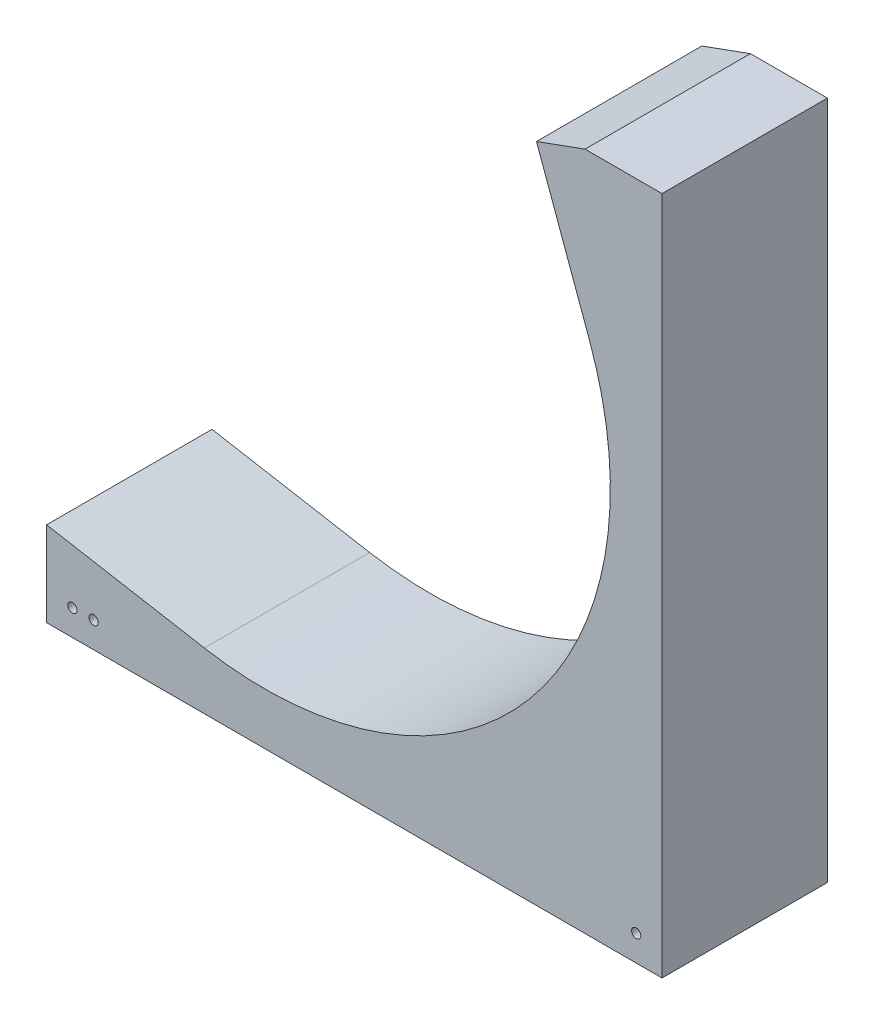
SolidWorks part; units mm, degrees
ref_plane "Front Plane" through (0, 0, 0) normal (0, 0, 1) x (1, 0, 0)
ref_plane "Top Plane" through (0, 0, 0) normal (0, 1, 0) x (1, 0, 0)
ref_plane "Right Plane" through (0, 0, 0) normal (1, 0, 0) x (0, 0, -1)
sketch "Sketch2" plane through (0, 0, 0) normal (0, 0, 1) x (1, 0, 0)
  line L0 (0, 0) -> (69.3863, 0)
  line L1 (69.3863, 0) -> (61.2697, 22.3003)
  line L2 (0, -65.2018) -> (-81.9123, -65.2018) construction
  line L3 (-11.3222, -64.2112) -> (-111.3786, -46.5686)
  line L4 (61.2697, 22.3003) -> (48.2387, 58.1026)
  arc A0 (61.2697, 22.3003) -> (-11.3222, -64.2112) centre (0, 0) cw
  circle A1 centre (0, 0) radius 45.212 construction
  point P11 (-11.3222, -64.2112)
  dimension "D3" = 90.424
  dimension "D1" = 65.2018
  dimension "D2" = 70
  dimension "D4" = 10
  dimension "D5" = 38.1
  dimension "D6" = 101.6
sketch3d "3DSketch1"
  line L0 (-114.819, -66.0796, 0) -> (-111.3786, -46.5686, 0) construction
  line L1 (-117.0243, -78.5867, -20.32) -> (-114.819, -66.0796, -20.32)
  line L2 (-117.0243, -78.5867, -20.32) -> (-117.0243, -78.5867, 20.32)
  line L3 (-117.0243, -78.5867, 20.32) -> (-114.819, -66.0796, 20.32)
  line L4 (-114.819, -66.0796, -20.32) -> (-114.819, -66.0796, 20.32)
  line L5 (-117.0243, -78.5867, -20.32) -> (-114.819, -66.0796, 20.32) construction
  line L6 (-117.0243, -78.5867, 20.32) -> (-114.819, -66.0796, -20.32) construction
  line L7 (-11.3222, -64.2112, 0) -> (-111.3786, -46.5686, 0) construction
  line L8 (0, -65.2018, 0) -> (-81.9123, -65.2018, 0) construction
  point P4 (-115.9216, -72.3331, 0)
  dimension "D1" = 12.7
  dimension "D2" = 40.64
  dimension "D3" = 19.812
sweep "Sweep3" add profiles "3DSketch1" path "Sketch2"
sketch "Sketch5" plane through (0, 0, 20.32) normal (0, 0, 1) x (1, 0, 0)
  line L0 (-117.0243, -78.5867) -> (-117.0243, -97.7138)
  line L1 (-117.0243, -97.7138) -> (97.7138, -97.7138)
  line L2 (97.7138, -97.7138) -> (97.7138, 69.2224)
  line L3 (97.7138, 69.2224) -> (78.79, 69.2224)
  line L4 (-117.0243, -78.5867) -> (-16.9678, -96.2293)
  line L5 (91.8209, 33.4201) -> (78.79, 69.2224)
  arc A0 (-16.9678, -96.2293) -> (91.8209, 33.4201) centre (0, 0) ccw construction
  arc A1 (-16.9678, -96.2293) -> (91.8209, 33.4201) centre (0, 0) ccw
  line M7 (-117.0243, -78.5867) -> (-16.9678, -96.2293)
extrude "Boss-Extrude1" add sketch "Sketch5" against normal up to surface (40.64 mm away) contours A1 L0 L1 M7 | A1 L1 L2 | A1 L2 L3 L5 up to face at (-65.8934, -81.1545, -20.32)
sketch "Sketch6" plane through (0, 0, 20.32) normal (0, 0, 1) x (1, 0, 0)
  circle A0 centre (91.3638, -91.3638) radius 1.1303 construction
  circle A1 centre (-41.9735, -91.3638) radius 1.1303 construction
  circle A2 centre (91.3638, -91.3638) radius 1.1303
  circle A3 centre (-41.9735, -91.3638) radius 1.1303
extrude "Cut-Extrude1" cut sketch "Sketch6" against normal through all
sketch "Sketch7" plane through (0, 0, 20.32) normal (0, 0, 1) x (1, 0, 0)
  line L0 (-117.0243, -78.5867) -> (-117.0243, -97.7138) construction
  line L1 (-117.0243, -97.7138) -> (97.7138, -97.7138) construction
  line L5 (-53.5243, -97.7138) -> (-127.1876, -97.7138)
  line L6 (-53.5243, -97.7138) -> (-53.5243, -24.0505)
  line L7 (-53.5243, -24.0505) -> (-127.1876, -24.0505)
  line L8 (-127.1876, -97.7138) -> (-127.1876, -24.0505)
  line L9 (-53.5243, -97.7138) -> (-127.1876, -24.0505) construction
  line L10 (-53.5243, -24.0505) -> (-127.1876, -97.7138) construction
  point P11 (-90.3559, -60.8821)
  dimension "D1" = 63.5
extrude "Cut-Extrude2" cut sketch "Sketch7" against normal through all
sketch "Sketch8" plane through (0, 0, 20.32) normal (0, 0, 1) x (1, 0, 0)
  line L0 (-53.5243, -97.7138) -> (97.7138, -97.7138) construction
  line L1 (-53.5243, -97.7138) -> (-53.5243, -76.8875) construction
  circle A0 centre (-47.1743, -91.3638) radius 1.1303
  dimension "D1" = 2.2606
  dimension "D2" = 6.35
  dimension "D3" = 6.35
extrude "Cut-Extrude3" cut sketch "Sketch8" against normal through all
